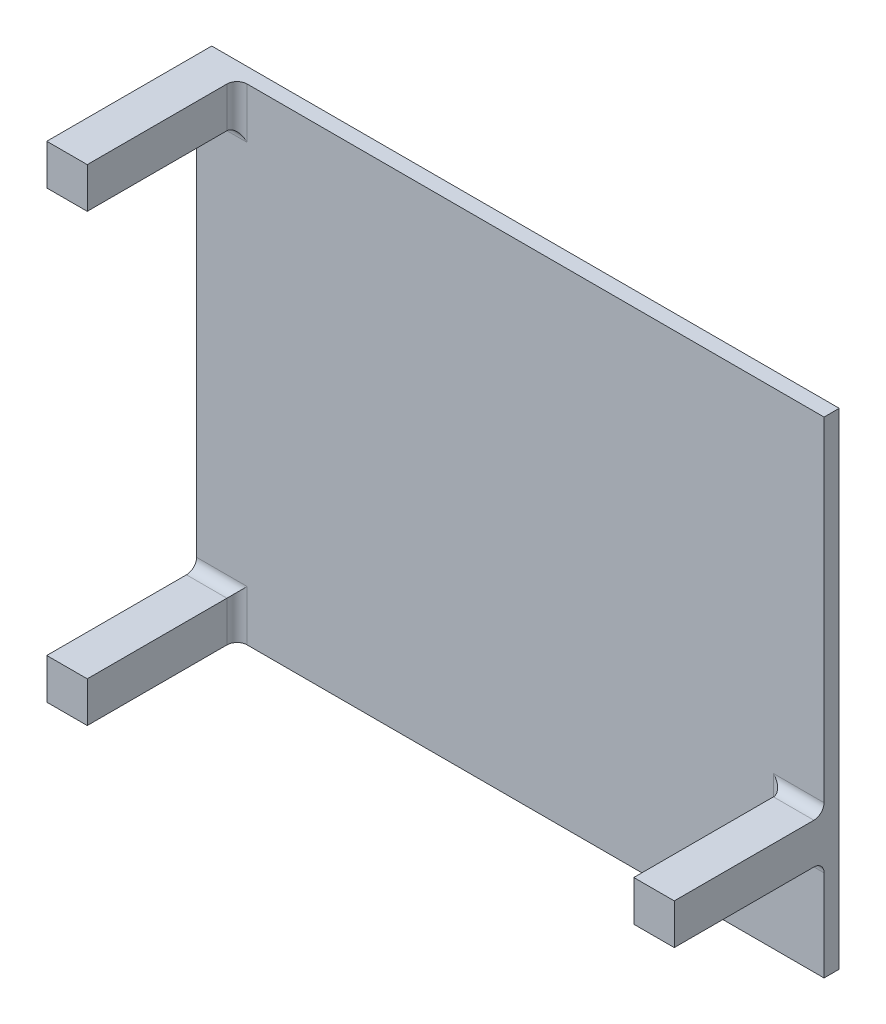
SolidWorks part; units mm, degrees
ref_plane "Ebene vorne" through (0, 0, 0) normal (0, 0, 1) x (1, 0, 0)
ref_plane "Ebene oben" through (0, 0, 0) normal (0, 1, 0) x (1, 0, 0)
ref_plane "Ebene rechts" through (0, 0, 0) normal (1, 0, 0) x (0, 0, -1)
sketch "Skizze1" plane through (0, 0, 0) normal (0, 0, 1) x (1, 0, 0)
  line L1 (-39.4336, 29.0766) -> (22.5664, 29.0766)
  line L2 (-39.4336, 29.0766) -> (-39.4336, -18.9234)
  line L3 (-39.4336, -18.9234) -> (22.5664, -18.9234)
  line L4 (22.5664, 29.0766) -> (22.5664, -18.9234)
  dimension "D1" = 62
  dimension "D2" = 48
extrude "Aufsatz-Linear austragen1" add sketch "Skizze1" along normal blind 1.5
sketch "Skizze3" plane through (0, 0, 1.5) normal (0, 0, 1) x (1, 0, 0)
  line L0 (22.5664, 29.0766) -> (-39.4336, 29.0766) construction
  line L1 (-39.4336, 29.0766) -> (-35.4336, 29.0766)
  line L2 (-39.4336, 29.0766) -> (-39.4336, 25.0766)
  line L3 (-39.4336, 25.0766) -> (-35.4336, 25.0766)
  line L4 (-35.4336, 29.0766) -> (-35.4336, 25.0766)
  line L5 (-39.4336, 29.0766) -> (-39.4336, -18.9234) construction
  line L6 (-39.4336, -18.9234) -> (22.5664, -18.9234) construction
  line L7 (-39.4336, -14.9234) -> (-35.4336, -14.9234)
  line L8 (-39.4336, -14.9234) -> (-39.4336, -18.9234)
  line L9 (-39.4336, -18.9234) -> (-35.4336, -18.9234)
  line L10 (-35.4336, -14.9234) -> (-35.4336, -18.9234)
  line L11 (22.5664, -18.9234) -> (22.5664, 29.0766) construction
  line L12 (22.5664, -4.9234) -> (18.5664, -4.9234)
  line L13 (22.5664, -4.9234) -> (22.5664, -8.9234)
  line L14 (22.5664, -8.9234) -> (18.5664, -8.9234)
  line L15 (18.5664, -4.9234) -> (18.5664, -8.9234)
  dimension "D1" = 4
  dimension "D2" = 4
  dimension "D3" = 4
  dimension "D4" = 4
  dimension "D5" = 4
  dimension "D6" = 4
  dimension "D7" = 10
extrude "Aufsatz-Linear austragen2" add sketch "Skizze3" along normal blind 14.8
fillet "Verrundung1" radius 1 7 edges at (20.5664, -4.9234, 1.5) (18.5664, -6.9234, 1.5) (20.5664, -8.9234, 1.5) (-37.4336, 25.0766, 1.5) (-35.4336, 27.0766, 1.5) (-35.4336, -16.9234, 1.5) (-37.4336, -14.9234, 1.5)
